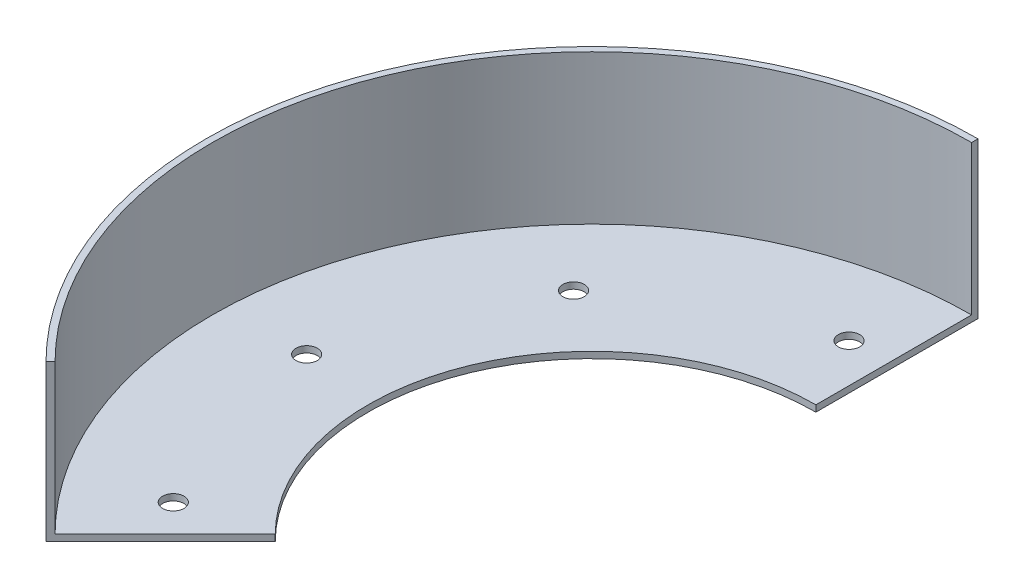
SolidWorks part; units mm, degrees
ref_plane "Front Plane" through (0, 0, 0) normal (0, 0, 1) x (1, 0, 0)
ref_plane "Top Plane" through (0, 0, 0) normal (0, 1, 0) x (1, 0, 0)
ref_plane "Right Plane" through (0, 0, 0) normal (1, 0, 0) x (0, 0, -1)
sketch "Sketch1" plane through (0, 0, 0) normal (0, 1, 0) x (1, 0, 0)
  line L2 (0, 105) -> (0, 181)
  line L3 (-127.9863, -127.9863) -> (-74.2462, -74.2462)
  arc A0 (0, 105) -> (-74.2462, -74.2462) centre (0, 0) ccw
  arc A2 (0, 181) -> (-127.9863, -127.9863) centre (0, 0) ccw
  dimension "D1" = 181
  dimension "D2" = 105
extrude "Boss-Extrude3" add sketch "Sketch1" along normal blind 3
sketch "Sketch5" plane through (0, 3, 0) normal (0, 1, 0) x (1, 0, 0)
  line L0 (-127.9863, -127.9863) -> (-74.2462, -74.2462) construction
  line L1 (0, 181) -> (0, 178)
  line L2 (-127.9863, -127.9863) -> (-125.865, -125.865)
  arc A0 (0, 181) -> (-127.9863, -127.9863) centre (0, 0) ccw
  arc A1 (0, 178) -> (-125.865, -125.865) centre (0, 0) ccw
  dimension "D1" = 3
extrude "Boss-Extrude4" add sketch "Sketch5" along normal blind 70
sketch "Sketch6" plane through (0, 3, 0) normal (0, 1, 0) x (1, 0, 0)
  line L0 (0, 0) -> (-111.0674, -85.225) construction
  line L1 (0, 0) -> (-139.8641, 6.1066) construction
  circle A0 centre (-139.8641, 6.1066) radius 5
  circle A5 centre (-111.0674, -85.225) radius 5
  circle A8 centre (-103.2169, 94.5808) radius 5
  circle A9 centre (-18.2733, 138.7996) radius 5
  dimension "D2" = 40
  dimension "D1" = 4
extrude "Cut-Extrude2" cut sketch "Sketch6" against normal blind 10
